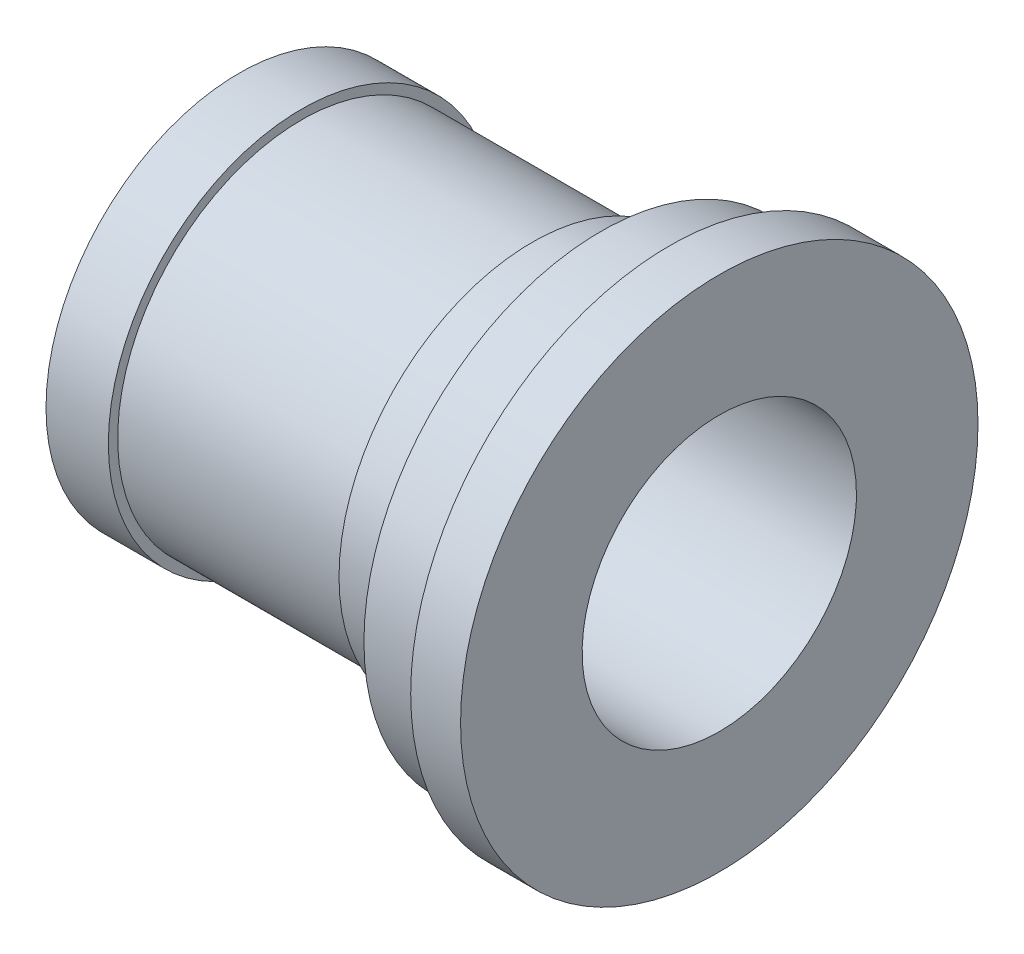
SolidWorks part; units mm, degrees
ref_plane "Front Plane" through (0, 0, 0) normal (0, 0, 1) x (1, 0, 0)
ref_plane "Top Plane" through (0, 0, 0) normal (0, 1, 0) x (1, 0, 0)
ref_plane "Right Plane" through (0, 0, 0) normal (1, 0, 0) x (0, 0, -1)
sketch "Sketch1" plane through (0, 0, 0) normal (1, 0, 0) x (0, 0, -1)
  line L0 (0, 58.7933) -> (0, -58.7933) construction
  circle A0 centre (0, 0) radius 22
  circle A1 centre (0, 0) radius 31
  dimension "D1" = 62
  dimension "D2" = 44
extrude "Boss-Extrude1" add sketch "Sketch1" along normal blind 10
sketch "Sketch2" plane through (10, 0, 0) normal (1, 0, 0) x (0, 0, -1)
  circle A0 centre (0, 0) radius 22
  circle A1 centre (0, 0) radius 29.5
  dimension "D1" = 59
  dimension "D2" = 44
extrude "Boss-Extrude2" add sketch "Sketch2" along normal blind 37
sketch "Sketch3" plane through (47, 0, 0) normal (1, 0, 0) x (0, 0, -1)
  circle A0 centre (0, 0) radius 22
  circle A1 centre (0, 0) radius 31
  dimension "D1" = 44
  dimension "D2" = 62
extrude "Boss-Extrude3" add sketch "Sketch3" along normal blind 11
sketch "Sketch4" plane through (58, 0, 0) normal (1, 0, 0) x (0, 0, -1)
  circle A0 centre (0, 0) radius 22
  circle A1 centre (0, 0) radius 38
  dimension "D1" = 44
  dimension "D2" = 76
extrude "Boss-Extrude4" add sketch "Sketch4" along normal blind 11
sketch "Sketch5" plane through (69, 0, 0) normal (1, 0, 0) x (0, 0, -1)
  circle A0 centre (0, 0) radius 22
  circle A1 centre (0, 0) radius 41.5
  dimension "D1" = 44
  dimension "D2" = 83
extrude "Boss-Extrude5" add sketch "Sketch5" along normal blind 8
sketch "Sketch6" plane through (0, 0, 0) normal (-1, 0, 0) x (0, 0, 1)
  circle A0 centre (-22, 0) radius 1.5
  circle A2 centre (0, 0) radius 22 construction
  dimension "D1" = 3
  dimension "D2" = 22
extrude "Cut-Extrude2" cut sketch "Sketch6" against normal blind 5 contours A0
